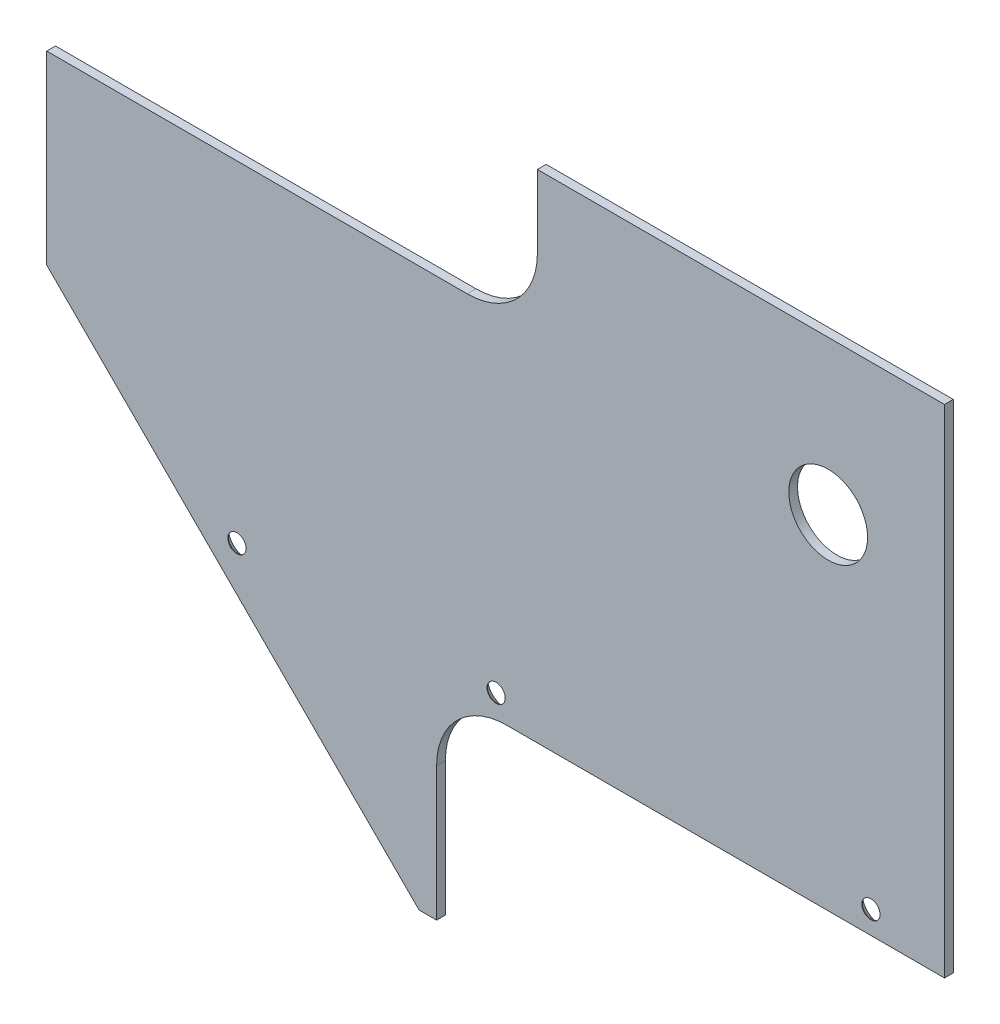
SolidWorks part; units mm, degrees
ref_plane "Front Plane" through (0, 0, 0) normal (0, 0, 1) x (1, 0, 0)
ref_plane "Top Plane" through (0, 0, 0) normal (0, 1, 0) x (1, 0, 0)
ref_plane "Right Plane" through (0, 0, 0) normal (1, 0, 0) x (0, 0, -1)
sketch "Sketch1" plane through (0, 0, 0) normal (0, 0, 1) x (1, 0, 0)
  line L0 (-138.2594, 48.9915) -> (32.2106, -121.4785)
  line L1 (32.2106, -121.4785) -> (222.7106, -121.4785)
  line L2 (-138.2594, 145.2215) -> (-138.2594, 48.9915)
  line L3 (-138.2594, 145.2215) -> (222.7106, 145.2215)
  line L4 (222.7106, -121.4785) -> (222.7106, 145.2215)
  circle A0 centre (180.538, 76.832) radius 14.2875
  circle A2 centre (180.538, 76.832) radius 64.9605 construction
  circle A3 centre (180.538, 76.832) radius 318.7974 construction
  point P0 (0, 0)
  point P2 (180.538, 76.832)
  dimension "D4" = 198.3105
  dimension "D1" = 45
  dimension "D2" = 266.7
  dimension "D5" = 245.11
extrude "Boss-Extrude1" add sketch "Sketch1" along normal blind 3.175
sketch "Sketch2" plane through (0, 0, 3.175) normal (0, 0, 1) x (1, 0, 0)
  line L0 (32.2106, -121.4785) -> (222.7106, -121.4785) construction
  line L1 (222.7634, -121.4785) -> (38.5606, -121.4785)
  line L2 (222.7634, -121.4785) -> (222.7634, -47.5645)
  line L3 (222.7634, -47.5645) -> (38.5606, -47.5645)
  line L4 (38.5606, -121.4785) -> (38.5606, -47.5645)
extrude "Cut-Extrude1" cut sketch "Sketch2" against normal through all contours L3 L4 L1 L2
fillet "Fillet1" radius 25.4 1 edges at (38.5606, -47.5645, 1.5875)
sketch "Sketch4" plane through (0, 0, 3.175) normal (0, 0, 1) x (1, 0, 0)
  line L1 (-138.2594, 145.2215) -> (-138.2594, 48.9915) construction
  line L3 (-138.2594, 145.2215) -> (75.1006, 145.2215)
  line L4 (-138.2594, 145.2215) -> (-138.2594, 80.7415)
  line L5 (-138.2594, 80.7415) -> (75.1006, 80.7415)
  line L6 (75.1006, 145.2215) -> (75.1006, 80.7415)
extrude "Cut-Extrude2" cut sketch "Sketch4" against normal through all contours L5 L6 L3 L4
fillet "Fillet2" radius 25.4 2 edges at (-138.2594, 80.7415, 1.5875) (75.1006, 80.7415, 1.5875)
sketch "Sketch7" plane through (0, 0, 3.175) normal (0, 0, 1) x (1, 0, 0)
  line L0 (222.7106, -47.5645) -> (222.7106, 145.2215) construction
  line L1 (75.1006, 145.2215) -> (222.7106, 145.2215)
  line L2 (75.1006, 145.2215) -> (75.1006, 132.5215)
  line L3 (75.1006, 132.5215) -> (222.7106, 132.5215)
  line L4 (222.7106, 145.2215) -> (222.7106, 132.5215)
  dimension "D1" = 12.7
extrude "Cut-Extrude4" cut sketch "Sketch7" against normal through all
hole_wizard "CSK for M6 Flat Head Machine Screw1" positions "Sketch9" profile "Sketch8" countersink size "M6" standard "ANSI Metric" end condition through all
sketch "Sketch9" plane through (0, 0, 0) normal (0, 0, -1) x (-1, 0, 0)
  line L1 (-222.7106, -47.5645) -> (-63.9606, -47.5645) construction
  line L5 (-222.7106, -47.5645) -> (-222.7106, 132.5215) construction
  point P0 (-196.0406, -39.3145)
  point P3 (-60.1506, -39.3145)
  point P6 (33.8294, -39.3145)
  dimension "D1" = 8.25
  dimension "D2" = 8.25
  dimension "D3" = 135.89
  dimension "D4" = 93.98
  dimension "D5" = 26.67
  dimension "D6" = 8.25
sketch "Sketch8" plane through (196.0406, -39.3145, 0) normal (1, 0, 0) x (0, 1, 0)
  line L0 (0, 0) -> (0, 3.175)
  line L1 (0, 3.175) -> (3.3, 3.175)
  line L2 (3.3, 3.175) -> (3.3, 3)
  line L3 (3.3, 3) -> (6.3, 0)
  line L5 (6.3, 0) -> (0, 0)
  line L6 (-3.3, 3) -> (-6.3, 0) construction
  line L11 (0, -6.35) -> (0, 107.95) construction
  dimension "Thru Hole Dia." = 6.6
  dimension "Thru Hole Depth" = 3.175
  dimension "Near C'Sink Dia." = 12.6
  dimension "Near C'Sink Angle" = 90
sketch "Sketch10" plane through (0, 0, 3.175) normal (0, 0, 1) x (1, 0, 0)
  line L1 (-102.7904, 87.751) -> (-160.6543, 87.751)
  line L2 (-102.7904, 87.751) -> (-102.7904, 13.5225)
  line L3 (-102.7904, 13.5225) -> (-160.6543, 13.5225)
  line L4 (-160.6543, 87.751) -> (-160.6543, 13.5225)
extrude "Cut-Extrude5" cut sketch "Sketch10" against normal through all
